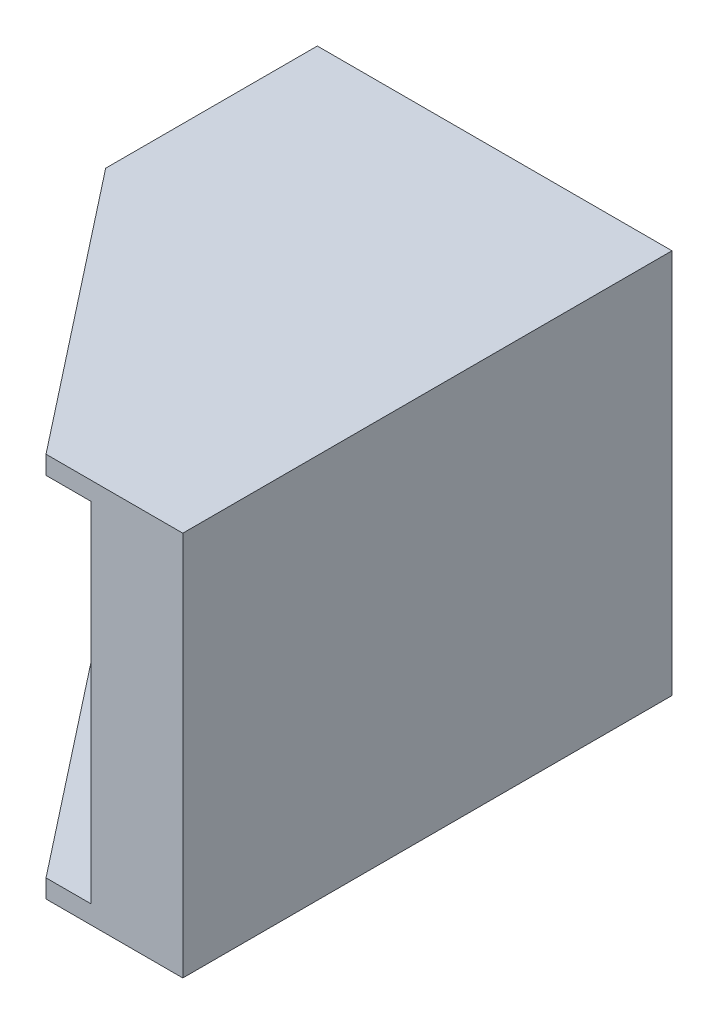
SolidWorks part; units mm, degrees
ref_plane "前视基准面" through (0, 0, 0) normal (0, 0, 1) x (1, 0, 0)
ref_plane "上视基准面" through (0, 0, 0) normal (0, 1, 0) x (1, 0, 0)
ref_plane "右视基准面" through (0, 0, 0) normal (1, 0, 0) x (0, 0, -1)
other "Configuration Table"
sketch "草图1" plane through (0, 0, 0) normal (0, 0, 1) x (1, 0, 0)
  line L1 (-63.8521, 33.085) -> (-5.8521, 33.085)
  line L2 (-63.8521, 33.085) -> (-63.8521, -29.915)
  line L3 (-63.8521, -29.915) -> (-5.8521, -29.915)
  line L4 (-5.8521, 33.085) -> (-5.8521, -29.915)
  dimension "D1" = 58
  dimension "D2" = 63
extrude "凸台-拉伸1" add sketch "草图1" along normal blind 60
sketch "草图3" plane through (0, 0, 60) normal (0, 0, 1) x (1, 0, 0)
  line L0 (-63.8521, 33.085) -> (-63.8521, -29.915) construction
  line L1 (-63.8521, 30.085) -> (-20.8521, 30.085)
  line L2 (-63.8521, 30.085) -> (-63.8521, -26.915)
  line L3 (-63.8521, -26.915) -> (-20.8521, -26.915)
  line L4 (-20.8521, 30.085) -> (-20.8521, -26.915)
  line L5 (-5.8521, 33.085) -> (-63.8521, 33.085) construction
  line L6 (-5.8521, -29.915) -> (-5.8521, 33.085) construction
  point P6 (-63.8521, 1.585)
  point P7 (-63.8521, 1.585)
  dimension "D1" = 3
  dimension "D2" = 15
extrude "切除-拉伸1" cut sketch "草图3" against normal blind 56
sketch "草图4" plane through (0, -29.915, 0) normal (0, -1, 0) x (1, 0, 0)
  line L0 (-63.8521, 60) -> (-63.8521, 14.6149)
  line L1 (-63.8521, 60) -> (-63.8521, 0) construction
  line L2 (-63.8521, 14.6149) -> (-28.222, 60)
  line L3 (-63.8521, 60) -> (-5.8521, 60) construction
  line L4 (-28.222, 60) -> (-63.8521, 60)
  point P8 (-63.8521, 14.6149)
extrude "切除-拉伸2" cut sketch "草图4" against normal through all
sketch "草图5" plane through (0, 0, 0) normal (0, 0, -1) x (-1, 0, 0)
  line L1 (5.8521, 33.085) -> (63.8521, 33.085)
  line L2 (5.8521, 33.085) -> (5.8521, -29.915)
  line L3 (5.8521, -29.915) -> (63.8521, -29.915)
  line L4 (63.8521, 33.085) -> (63.8521, -29.915)
extrude "凸台-拉伸2" add sketch "草图5" along normal blind 20
